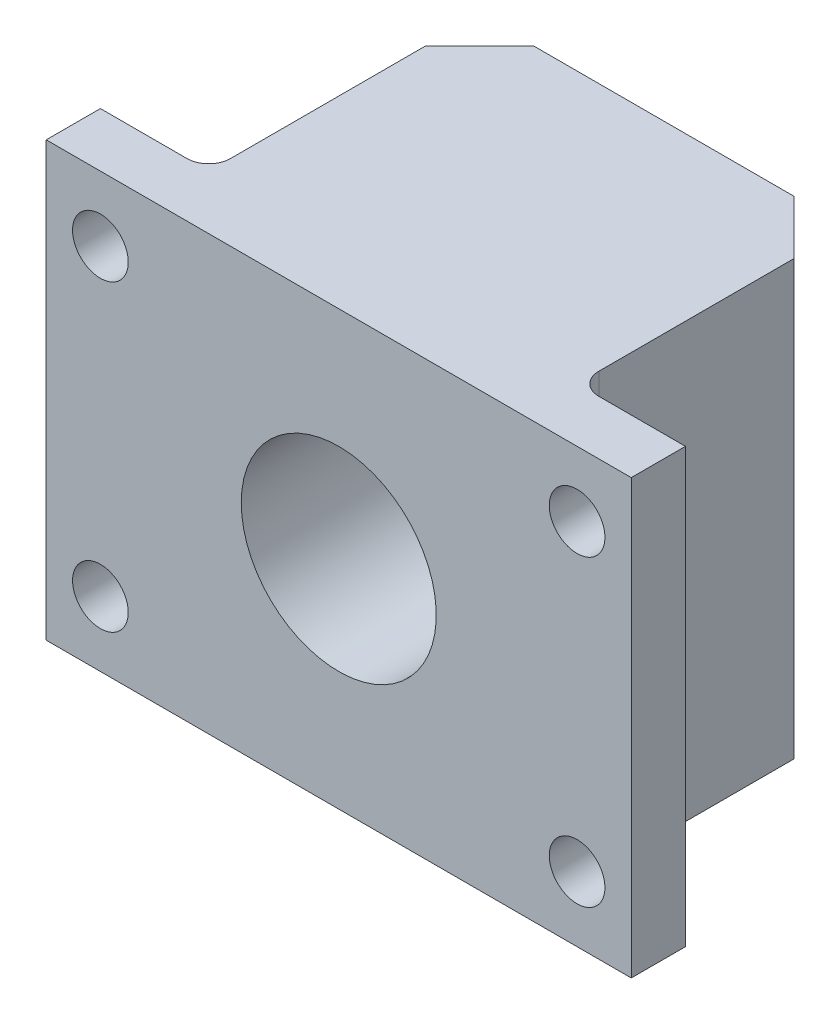
SolidWorks part; units mm, degrees
ref_plane "Front Plane" through (0, 0, 0) normal (0, 0, 1) x (1, 0, 0)
ref_plane "Top Plane" through (0, 0, 0) normal (0, 1, 0) x (1, 0, 0)
ref_plane "Right Plane" through (0, 0, 0) normal (1, 0, 0) x (0, 0, -1)
sketch "Sketch4" plane through (0, 0, 0) normal (0, 1, 0) x (1, 0, 0)
  line L4 (0, 0) -> (0, 19.05) construction
  line L7 (-10.795, 3.175) -> (-17.145, 3.175)
  line L9 (-17.145, 0) -> (-12.7, 0)
  line L10 (17.145, 0) -> (12.7, 0)
  line L11 (17.145, 3.175) -> (17.145, 0)
  line L12 (10.795, 3.175) -> (17.145, 3.175)
  line L13 (-17.145, 3.175) -> (-17.145, 0)
  line L14 (-12.7, 0) -> (12.7, 0)
  line L16 (-10.795, 19.05) -> (10.795, 19.05)
  line L18 (10.795, 19.05) -> (10.795, 3.175)
  line L19 (-10.795, 19.05) -> (-10.795, 3.175)
  point P4 (0, 0)
  dimension "D1" = 25.4
  dimension "D2" = 19.05
  dimension "D3" = 3.175
  dimension "D4" = 6.35
  dimension "D5" = 21.59
extrude "Boss-Extrude4" add sketch "Sketch4" along normal blind 25.4
chamfer "Chamfer1" distance 3.175 distance2 3.175 2 edges at (10.795, 12.7, -19.05) (-10.795, 12.7, -19.05)
sketch "Sketch10" plane through (0, 0, -3.175) normal (0, 0, -1) x (-1, 0, 0)
  line L0 (-17.145, 25.4) -> (-10.795, 25.4) construction
  line L1 (-17.145, 12.7) -> (17.145, 12.7) construction
  line L2 (-17.145, 25.4) -> (-17.145, 0) construction
  line L3 (17.145, 25.4) -> (17.145, 0) construction
  line L4 (0, 25.4) -> (0, 0) construction
  line L5 (-7.62, 25.4) -> (7.62, 25.4) construction
  circle A0 centre (-13.97, 21.59) radius 1.632
  circle A1 centre (-13.97, 3.81) radius 1.632
  circle A2 centre (13.97, 3.81) radius 1.6319
  circle A3 centre (13.97, 21.59) radius 1.6319
  point P4 (-13.97, 25.4)
  dimension "D1" = 3.2639
  dimension "D2" = 3.81
extrude "Cut-Extrude3" cut sketch "Sketch10" against normal up to surface (3.175 mm away) up to face at (0, 12.7, 0)
sketch "Sketch11" plane through (0, 0, -19.05) normal (0, 0, -1) x (-1, 0, 0)
  line L0 (0, 25.4) -> (0, 0) construction
  line L1 (-7.62, 25.4) -> (7.62, 25.4) construction
  line L2 (-7.62, 12.7) -> (7.62, 12.7) construction
  line L3 (-7.62, 25.4) -> (-7.62, 0) construction
  line L4 (7.62, 0) -> (7.62, 25.4) construction
  circle A0 centre (0, 12.7) radius 5.715
  dimension "D1" = 11.43
extrude "Cut-Extrude4" cut sketch "Sketch11" against normal through all
fillet "Fillet1" radius 1.27 2 edges at (-10.795, 12.7, -3.175) (10.795, 12.7, -3.175)
